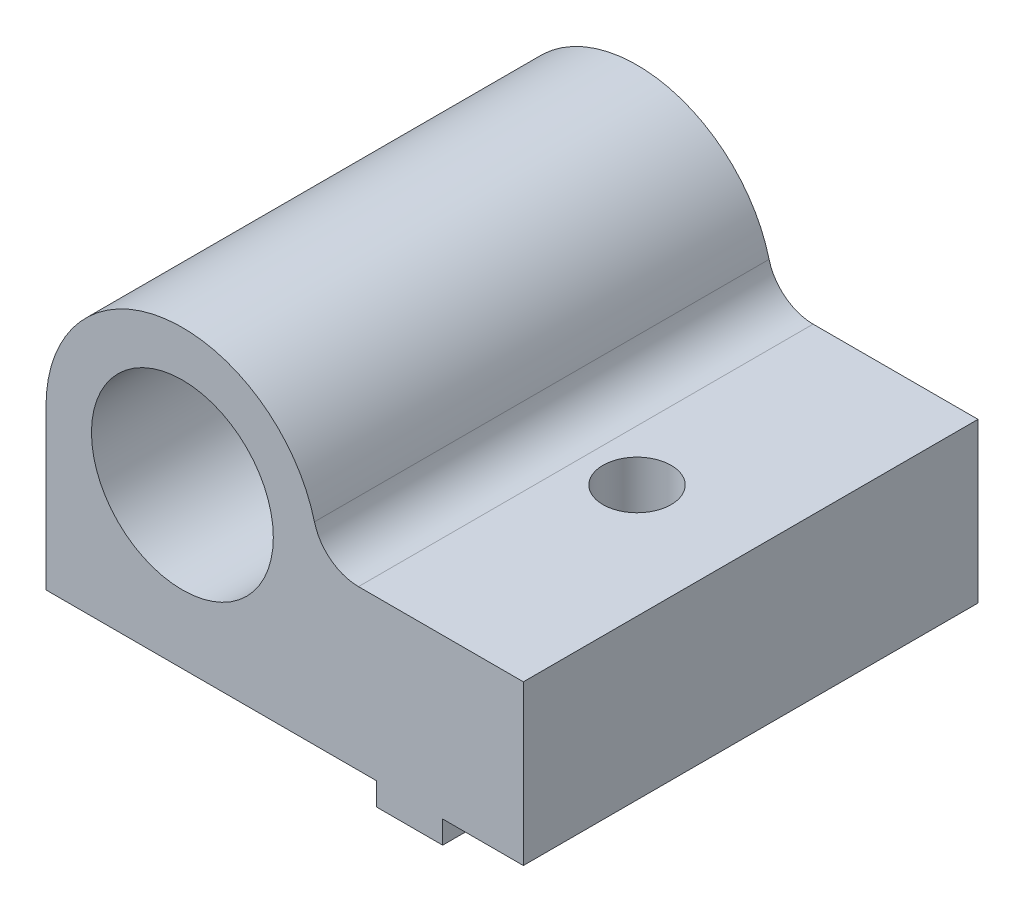
SolidWorks part; units mm, degrees
ref_plane "Front Plane" through (0, 0, 0) normal (0, 0, 1) x (1, 0, 0)
ref_plane "Top Plane" through (0, 0, 0) normal (0, 1, 0) x (1, 0, 0)
ref_plane "Right Plane" through (0, 0, 0) normal (1, 0, 0) x (0, 0, -1)
sketch "Sketch1" plane through (0, 0, 0) normal (0, 0, 1) x (1, 0, 0)
  line L0 (-6, 0) -> (-6, -7)
  line L1 (15, -7) -> (15, 0)
  line L3 (-6, -7) -> (15, -7)
  line L4 (15, 0) -> (6, 0)
  arc A0 (-6, 0) -> (6, 0) centre (0, 0) cw
  circle A1 centre (0, 0) radius 4
  point P1 (0, 0)
  point P5 (0, 0)
  dimension "D1" = 8
  dimension "D2" = 6
  dimension "D3" = 7
  dimension "D4" = 7
  dimension "D5" = 21
  dimension "D6" = 9
extrude "Main" add sketch "Sketch1" along normal mid plane 20
sketch "Sketch3" plane through (0, -7, 0) normal (0, -1, 0) x (-1, 0, 0)
  line L1 (-8.55, -10) -> (-11.45, -10)
  line L2 (-8.55, -10) -> (-8.55, 10)
  line L3 (-8.55, 10) -> (-11.45, 10)
  line L4 (-11.45, -10) -> (-11.45, 10)
  line L7 (6, 10) -> (-15, 10) construction
  line L8 (6, -10) -> (-15, -10) construction
  line L10 (-15, -10) -> (-15, 10) construction
  point P4 (-7.0456, -10)
  point P9 (-10, 10)
  dimension "D1" = 2.9
  dimension "D2" = 5
extrude "MakerBeamRectangularGuide" add sketch "Sketch3" along normal blind 1
sketch "Sketch4" plane through (0, 0, 0) normal (0, 1, 0) x (1, 0, 0)
  line L1 (15, -10) -> (15, 10) construction
  circle A0 centre (10, 0) radius 1.5
  point P2 (0, 0)
  dimension "D1" = 3
  dimension "D3" = 5
extrude "MakerBeamFixHole" cut sketch "Sketch4" against normal through all
fillet "Fillet1" radius 2 1 edges at (6, 0, 0)
